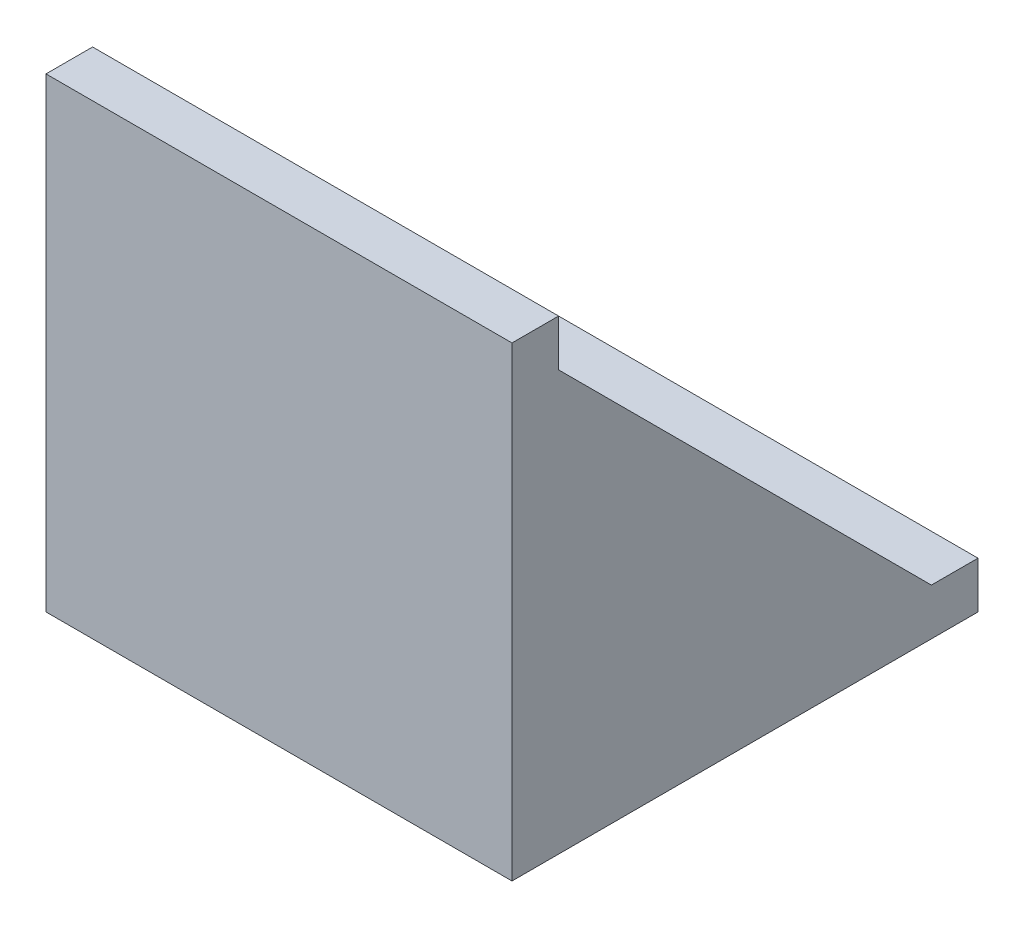
SolidWorks part; units mm, degrees
ref_plane "前视基准面" through (0, 0, 0) normal (0, 0, 1) x (1, 0, 0)
ref_plane "上视基准面" through (0, 0, 0) normal (0, 1, 0) x (1, 0, 0)
ref_plane "右视基准面" through (0, 0, 0) normal (1, 0, 0) x (0, 0, -1)
sketch "草图1" plane through (0, 0, 0) normal (1, 0, 0) x (0, 0, -1)
  line L2 (-6.0269, -0.3446) -> (-26.0269, -0.3446)
  line L3 (-26.0269, -0.3446) -> (-26.0269, 19.6554)
  line L4 (-26.0269, 19.6554) -> (-24.0269, 19.6554)
  line L5 (-6.0269, -0.3446) -> (-6.0269, 1.6554)
  line L6 (-24.0269, 17.6554) -> (-24.0269, 19.6554)
  line L7 (-6.0269, 1.6554) -> (-8.0269, 1.6554)
  line L8 (-24.0269, 17.6554) -> (-8.0269, 1.6554)
  dimension "D1" = 2
  dimension "D2" = 20
  dimension "D3" = 20
  dimension "D4" = 2
  dimension "D5" = 2
  dimension "D6" = 2
extrude "凸台-拉伸1" add sketch "草图1" along normal blind 20 from offset 0
sketch "草图3" plane through (0, -0.3446, 0) normal (0, -1, 0) x (1, 0, 0)
  line L5 (20, 8.0269) -> (0, 8.0269) construction
  line L6 (1, 8.0269) -> (19, 8.0269)
  line L7 (1, 8.0269) -> (1, 24.0269)
  line L8 (20, 24.0269) -> (0, 24.0269) construction
  line L9 (1, 24.0269) -> (19, 24.0269)
  line L10 (20, 24.0269) -> (0, 24.0269) construction
  line L11 (19, 24.0269) -> (19, 8.0269)
  dimension "D2" = 18
extrude "切除-拉伸1" cut sketch "草图3" against normal blind 16 from surface at -2 starting at face at (10, 1.6554, 7.0269)
